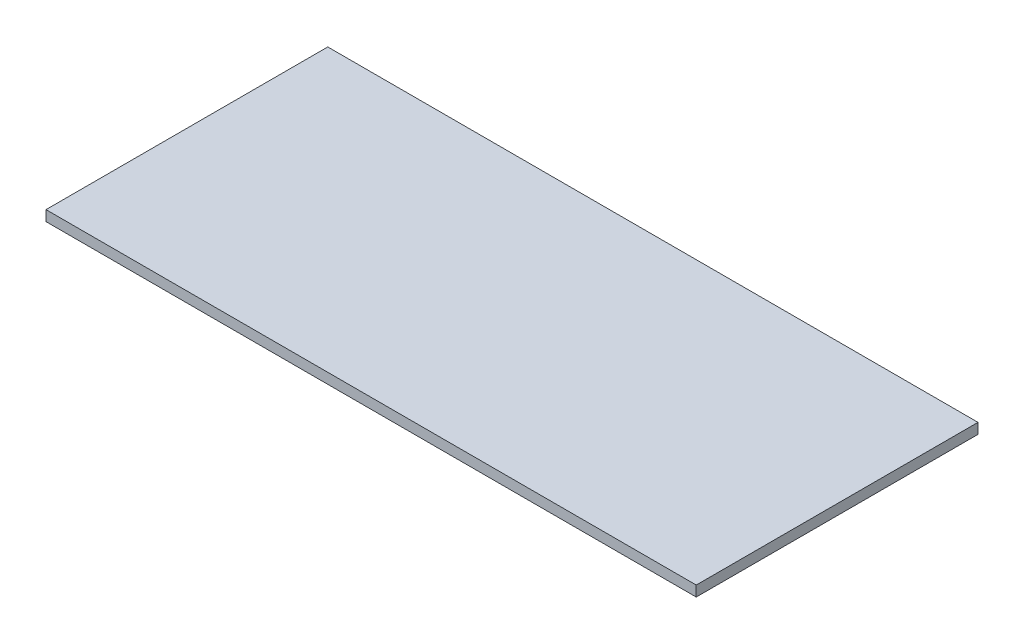
SolidWorks part; units mm, degrees
ref_plane "Front Plane" through (0, 0, 0) normal (0, 0, 1) x (1, 0, 0)
ref_plane "Top Plane" through (0, 0, 0) normal (0, 1, 0) x (1, 0, 0)
ref_plane "Right Plane" through (0, 0, 0) normal (1, 0, 0) x (0, 0, -1)
sketch "Sketch1" plane through (0, 0, 0) normal (0, 1, 0) x (1, 0, 0)
  line L1 (190.5, -82.55) -> (-190.5, -82.55)
  line L2 (190.5, -82.55) -> (190.5, 82.55)
  line L3 (190.5, 82.55) -> (-190.5, 82.55)
  line L4 (-190.5, -82.55) -> (-190.5, 82.55)
  line L5 (190.5, -82.55) -> (-190.5, 82.55) construction
  line L6 (190.5, 82.55) -> (-190.5, -82.55) construction
  point P0 (0, 0)
  dimension "D1" = 165.1
  dimension "D2" = 381
extrude "Boss-Extrude1" add sketch "Sketch1" along normal blind 6.11
